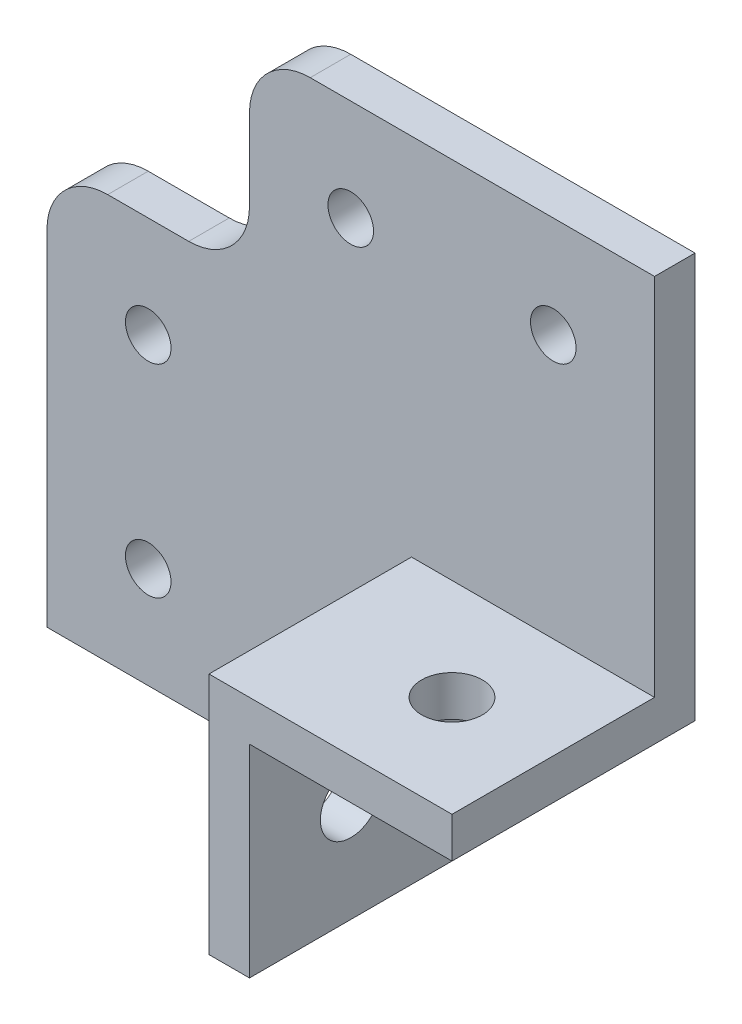
SolidWorks part; units mm, degrees
ref_plane "Plan de face" through (0, 0, 0) normal (0, 0, 1) x (1, 0, 0)
ref_plane "Plan de dessus" through (0, 0, 0) normal (0, 1, 0) x (1, 0, 0)
ref_plane "Plan de droite" through (0, 0, 0) normal (1, 0, 0) x (0, 0, -1)
sketch "Esquisse1" plane through (0, 0, 0) normal (0, 0, 1) x (1, 0, 0)
  line L0 (-20, 60) -> (-20, 40)
  line L1 (-20, 40) -> (-40, 40)
  line L2 (-40, 40) -> (-40, 0)
  line L3 (-40, 0) -> (0, 0)
  line L4 (0, 0) -> (0, 20)
  line L5 (0, 20) -> (20, 20)
  line L6 (20, 20) -> (20, 60)
  line L7 (20, 60) -> (-20, 60)
  dimension "D1" = 20
  dimension "D2" = 20
  dimension "D3" = 60
  dimension "D4" = 40
  dimension "D5" = 60
  dimension "D6" = 40
extrude "Boss.-Extru.1" add sketch "Esquisse1" along normal blind 4
sketch "Esquisse2" plane through (0, 0, 4) normal (0, 0, 1) x (1, 0, 0)
  line L0 (20, 20) -> (20, 24)
  line L1 (20, 20) -> (20, 60) construction
  line L2 (20, 24) -> (-4, 24)
  line L3 (-4, 24) -> (-4, 0)
  line L4 (-40, 0) -> (0, 0) construction
  line L5 (-4, 0) -> (0, 0)
  line L6 (0, 0) -> (0, 20)
  line L7 (0, 20) -> (20, 20)
  dimension "D1" = 4
  dimension "D2" = 4
extrude "Boss.-Extru.2" add sketch "Esquisse2" along normal blind 20
sketch "Esquisse3" plane through (-4, 0, 0) normal (-1, 0, 0) x (0, 0, 1)
  line L0 (24, 24) -> (24, 0) construction
  line L1 (24, 0) -> (4, 0) construction
  circle A0 centre (14, 10) radius 3
  dimension "D1" = 6
  dimension "D2" = 10
  dimension "D3" = 10
extrude "Enlèv. mat.-Extru.1" cut sketch "Esquisse3" against normal through all
sketch "Esquisse4" plane through (0, 24, 0) normal (0, 1, 0) x (1, 0, 0)
  line L0 (20, -24) -> (-4, -24) construction
  line L1 (20, -24) -> (20, -4) construction
  circle A0 centre (10, -14) radius 3
  dimension "D1" = 6
  dimension "D2" = 10
  dimension "D3" = 10
extrude "Enlèv. mat.-Extru.2" cut sketch "Esquisse4" against normal through all
sketch "Esquisse5" plane through (0, 0, 4) normal (0, 0, 1) x (1, 0, 0)
  line L0 (-20, 60) -> (-20, 40) construction
  line L1 (20, 60) -> (-20, 60) construction
  line L2 (20, 24) -> (20, 60) construction
  line L3 (-20, 40) -> (-40, 40) construction
  line L4 (-40, 40) -> (-40, 0) construction
  line L5 (-40, 0) -> (-4, 0) construction
  circle A0 centre (10, 50) radius 2.25
  circle A1 centre (-10, 50) radius 2.25
  circle A2 centre (-30, 30) radius 2.25
  circle A3 centre (-30, 10) radius 2.25
  dimension "D1" = 4.5
  dimension "D2" = 4.5
  dimension "D3" = 10
  dimension "D4" = 10
  dimension "D5" = 10
  dimension "D6" = 10
  dimension "D7" = 4.5
  dimension "D8" = 4.5
  dimension "D9" = 10
  dimension "D10" = 10
  dimension "D11" = 10
  dimension "D12" = 10
extrude "Enlèv. mat.-Extru.3" cut sketch "Esquisse5" against normal through all
fillet "Congé1" radius 6 3 edges at (-20, 40, 2) (-20, 60, 2) (-40, 40, 2)
